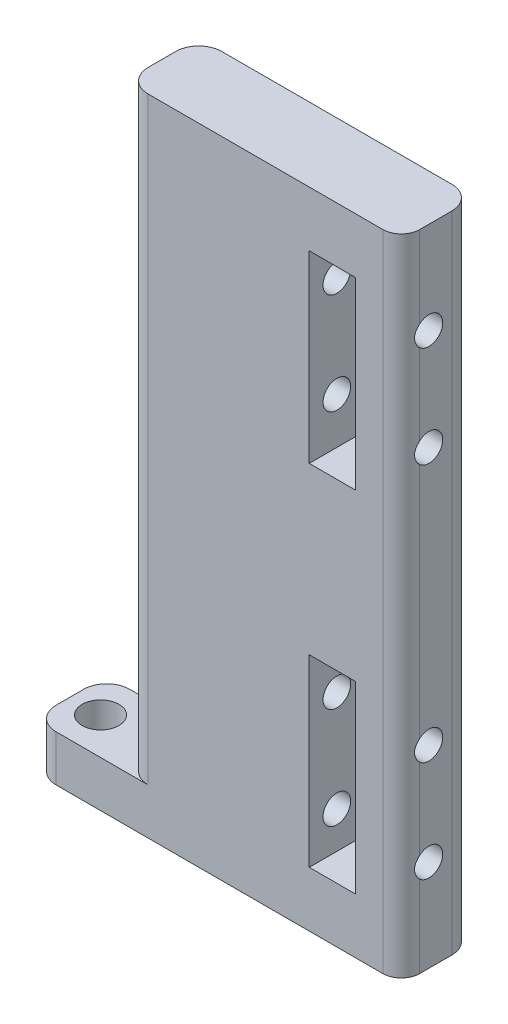
SolidWorks part; units mm, degrees
material "ABS"
ref_plane "Plano frontal" through (0, 0, 0) normal (0, 0, 1) x (1, 0, 0)
ref_plane "Plano superior" through (0, 0, 0) normal (0, 1, 0) x (1, 0, 0)
ref_plane "Plano direito" through (0, 0, 0) normal (1, 0, 0) x (0, 0, -1)
sketch "Esboço2" plane through (0, 0, 0) normal (0, 0, 1) x (1, 0, 0)
  line L1 (-67.2812, 34.8924) -> (-37.2812, 34.8924)
  line L2 (-67.2812, 34.8924) -> (-67.2812, -35.1076)
  line L3 (-67.2812, -35.1076) -> (-37.2812, -35.1076)
  line L4 (-37.2812, 34.8924) -> (-37.2812, -35.1076)
extrude "Ressalto-extrusão1" add sketch "Esboço2" along normal blind 8
sketch "Esboço3" plane through (0, -35.1076, 0) normal (0, -1, 0) x (-1, 0, 0)
  line L0 (50.5731, -0.27) -> (50.5731, -7.73) construction
  line L1 (50.5731, -7.73) -> (50.1981, -7.73) construction
  line L3 (55.6594, -4) -> (67.2812, -4) construction
  line L4 (67.2812, -8) -> (67.2812, 0) construction
  line L5 (67.2812, 0) -> (37.2812, 0) construction
  line L7 (50.5731, -7.73) -> (50.9481, -7.73) construction
  circle A5 centre (58.2812, -4) radius 0.75
  circle A7 centre (63.2812, -4) radius 0.75
  dimension "D1" = 4
  dimension "D2" = 5
  dimension "D7" = 7.46
  dimension "D8" = 0.27
  dimension "D9" = 0
extrude "Corte-extrusão1" cut sketch "Esboço3" against normal blind 30
fillet "Filete1" radius 2 1 edges at (-37.2812, -0.1076, 8)
sketch "Esboço17" plane through (0, 0, 0) normal (0, 0, -1) x (-1, 0, 0)
  line L1 (67.2812, -35.1076) -> (77.2812, -35.1076)
  line L2 (67.2812, -35.1076) -> (67.2812, -30.1076)
  line L3 (67.2812, -30.1076) -> (77.2812, -30.1076)
  line L4 (77.2812, -35.1076) -> (77.2812, -30.1076)
extrude "Ressalto-extrusão4" add sketch "Esboço17" against normal blind 8
sketch "Esboço20" plane through (0, -35.1076, 0) normal (0, -1, 0) x (1, 0, 0)
  line L0 (-77.2812, 8) -> (-39.2812, 8) construction
  circle A0 centre (-73.9512, 4) radius 2
  circle A1 centre (-63.2812, 4) radius 0.75 construction
  dimension "D1" = 4
  dimension "D2" = 10.67
extrude "Corte-extrusão9" cut sketch "Esboço20" against normal blind 8 contours A0
fillet "Filete2" radius 2.5 1 edges at (-67.2812, 2.3924, 8)
fillet "Filete3" radius 2.5 1 edges at (-67.2812, 2.3924, 0)
fillet "Filete4" radius 2.5 1 edges at (-77.2812, -32.6076, 8)
fillet "Filete5" radius 2.5 1 edges at (-77.2812, -32.6076, 0)
sketch "Esboço21" plane through (0, 0, 8) normal (0, 0, 1) x (1, 0, 0)
  line L0 (-39.2812, 34.8924) -> (-64.7812, 34.8924) construction
  line L1 (-47.2812, 28.8924) -> (-42.2812, 28.8924)
  line L2 (-47.2812, 28.8924) -> (-47.2812, 8.8924)
  line L3 (-47.2812, 8.8924) -> (-42.2812, 8.8924)
  line L4 (-42.2812, 28.8924) -> (-42.2812, 8.8924)
  line L5 (-39.2812, -35.1076) -> (-39.2812, 34.8924) construction
  line L6 (-74.7812, -35.1076) -> (-39.2812, -35.1076) construction
  line L7 (-42.2812, -29.1076) -> (-47.2812, -29.1076)
  line L8 (-42.2812, -29.1076) -> (-42.2812, -9.1076)
  line L9 (-42.2812, -9.1076) -> (-47.2812, -9.1076)
  line L10 (-47.2812, -29.1076) -> (-47.2812, -9.1076)
  dimension "D1" = 6
  dimension "D2" = 20
  dimension "D3" = 3
  dimension "D4" = 5
  dimension "D5" = 6
  dimension "D6" = 20
  dimension "D7" = 5
  dimension "D8" = 3
extrude "Corte-extrusão10" cut sketch "Esboço21" against normal through all
fillet "Filete6" radius 2.5 1 edges at (-37.2812, -0.1076, 0)
sketch "Esboço22" plane through (-37.2812, 0, 0) normal (1, 0, 0) x (0, 0, -1)
  line L0 (-6, -35.1076) -> (-2.5, -35.1076) construction
  line L1 (-6, 34.8924) -> (-2.5, 34.8924) construction
  line L2 (-8, -35.1076) -> (-8, 34.8924) construction
  circle A0 centre (-5, -25.1076) radius 1.5
  circle A1 centre (-5, -14.1076) radius 1.5
  circle A2 centre (-5, 24.8924) radius 1.5
  circle A3 centre (-5, 13.8924) radius 1.5
  dimension "D1" = 3
  dimension "D2" = 3
  dimension "D3" = 10
  dimension "D4" = 11
  dimension "D5" = 3
  dimension "D6" = 3
  dimension "D7" = 10
  dimension "D8" = 11
  dimension "D9" = 3
  dimension "D10" = 3
extrude "Corte-extrusão11" cut sketch "Esboço22" against normal blind 20
